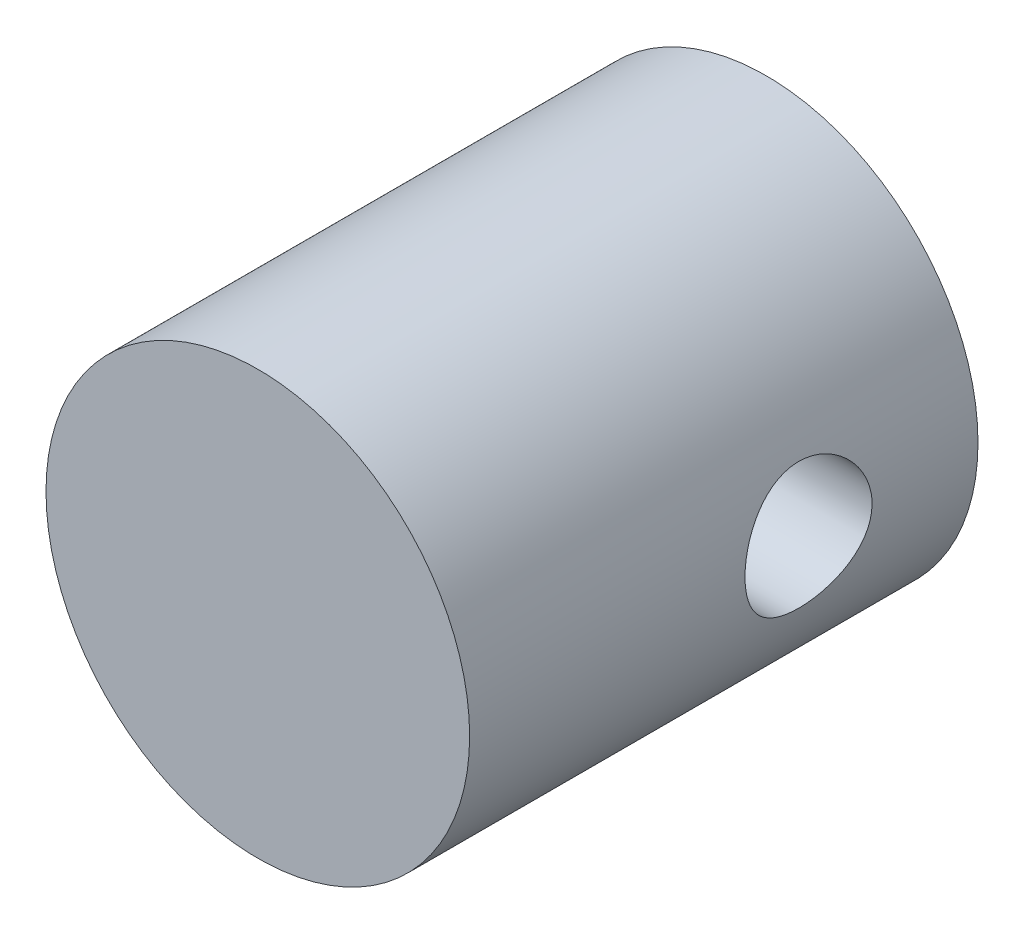
SolidWorks part; units mm, degrees
ref_plane "Front Plane" through (0, 0, 0) normal (0, 0, 1) x (1, 0, 0)
ref_plane "Top Plane" through (0, 0, 0) normal (0, 1, 0) x (1, 0, 0)
ref_plane "Right Plane" through (0, 0, 0) normal (1, 0, 0) x (0, 0, -1)
sketch "Sketch1" plane through (0, 0, 0) normal (0, 0, 1) x (1, 0, 0)
  circle A0 centre (0, 0) radius 2.5
  dimension "D1" = 5
extrude "Boss-Extrude1" add sketch "Sketch1" along normal blind 6 contours A0
sketch "Sketch2" plane through (0, 0, 0) normal (1, 0, 0) x (0, 0, -1)
  line L0 (2.75, 0) -> (-2.75, 0) construction
  line L1 (0, 2.75) -> (0, -2.75) construction
  circle A0 centre (-2, 0) radius 0.75
  dimension "D2" = 1.5
  dimension "D1" = 2
extrude "Cut-Extrude1" cut sketch "Sketch2" against normal through all both and the other way through all contours A0
